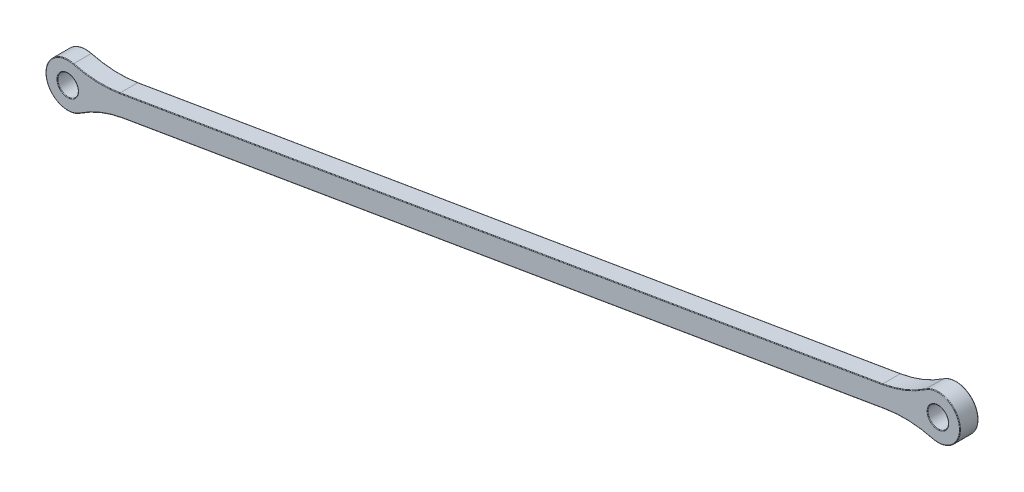
SolidWorks part; units mm, degrees
ref_plane "Front Plane" through (0, 0, 0) normal (0, 0, 1) x (1, 0, 0)
ref_plane "Top Plane" through (0, 0, 0) normal (0, 1, 0) x (1, 0, 0)
ref_plane "Right Plane" through (0, 0, 0) normal (1, 0, 0) x (0, 0, -1)
sketch "Sketch1" plane through (0, 0, 0) normal (0, 0, 1) x (1, 0, 0)
  line L0 (-71.3526, 303.2131) -> (-307.9763, 263.098) construction
  line L1 (-71.3526, 303.2131) -> (-307.9763, 263.098) construction
  line L2 (-307.9763, 263.098) -> (-71.3526, 303.2131) construction
  line L3 (-308.4443, 265.8586) -> (-71.8206, 305.9737)
  line L4 (-307.5083, 260.3374) -> (-70.8846, 300.4525)
  arc A0 (-308.4443, 265.8586) -> (-307.5083, 260.3374) centre (-307.9763, 263.098) ccw
  arc A1 (-70.8846, 300.4525) -> (-71.8206, 305.9737) centre (-71.3526, 303.2131) ccw
  circle A2 centre (-307.9763, 263.098) radius 6
  circle A3 centre (-71.3526, 303.2131) radius 6
  arc A4 (-308.4443, 265.8586) -> (-307.5083, 260.3374) centre (-307.9763, 263.098) cw
  arc A5 (-71.8206, 305.9737) -> (-70.8846, 300.4525) centre (-71.3526, 303.2131) ccw
  point P3 (-189.6644, 283.1555)
  dimension "D2" = 12
  dimension "D1" = 5.6
extrude "Boss-Extrude1" add sketch "Sketch1" against normal blind 5 contours L3 A2 L4 A0 | L3 A4 L4 A2 | L4 A3 L3 A1 | A5 L3 A3 L4 | A3 L3 A2 L4
fillet "Fillet1" radius 30 4 edges at (-302.2763, 261.2244, -2.5) (-76.1165, 299.5655, -2.5) (-77.0525, 305.0867, -2.5) (-303.2123, 266.7456, -2.5)
fillet "Fillet2" radius 0.15 20 edges at (-305.1763, 263.098, 0) (-80.3268, 305.2155, 0) (-65.437, 304.216, 0) (-79.1653, 298.3648, 0) (-189.1964, 280.3949, 0) (-299.0021, 261.0956, 0) (-313.8919, 262.0951, 0) (-300.1635, 267.9463, 0) (-190.1324, 285.9161, 0) (-68.5526, 303.2131, 0) (-305.1763, 263.098, -5) (-299.0021, 261.0956, -5) (-189.1964, 280.3949, -5) (-79.1653, 298.3648, -5) (-65.437, 304.216, -5) (-80.3268, 305.2155, -5) (-190.1324, 285.9161, -5) (-300.1635, 267.9463, -5) (-313.8919, 262.0951, -5) (-68.5526, 303.2131, -5)
